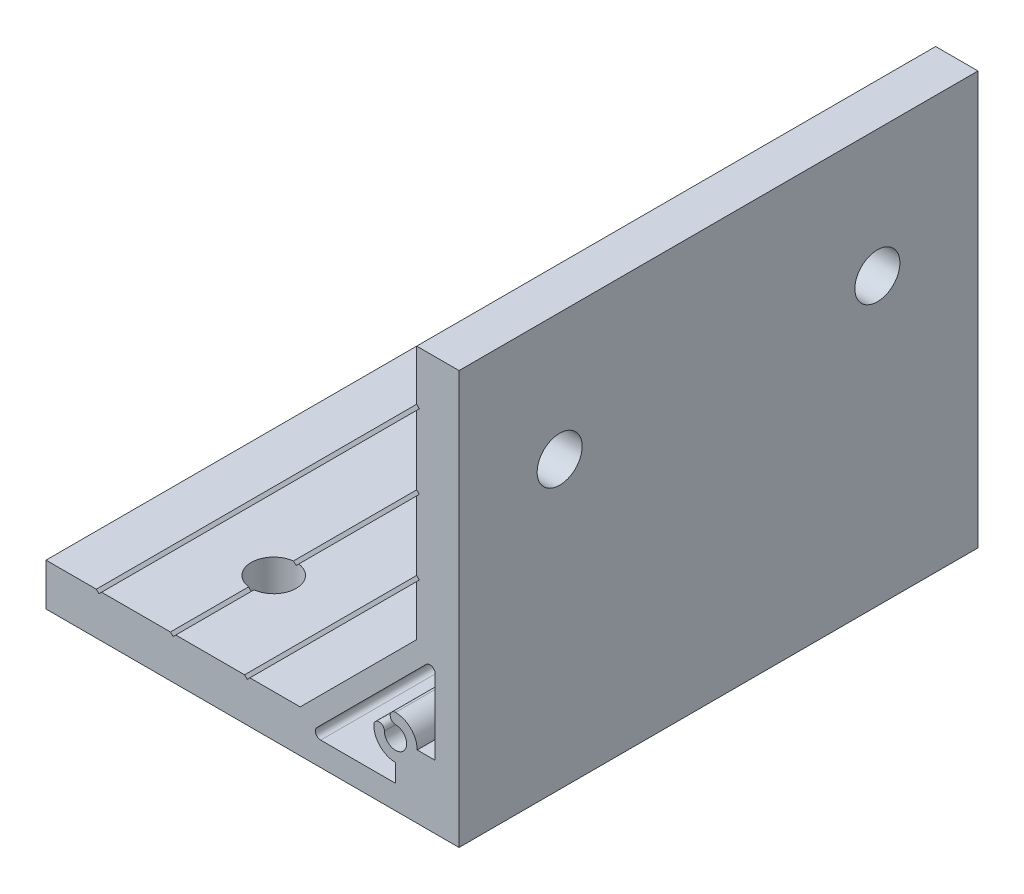
SolidWorks part; units mm, degrees
material "6063 T5"
ref_plane "Спереди" through (0, 0, 0) normal (0, 0, 1) x (1, 0, 0)
ref_plane "Сверху" through (0, 0, 0) normal (0, 1, 0) x (1, 0, 0)
ref_plane "Справа" through (0, 0, 0) normal (1, 0, 0) x (0, 0, -1)
sketch "Эскиз1" plane through (0, 0, 0) normal (0, 0, 1) x (1, 0, 0)
  line L0 (-78, 0) -> (0, 0)
  line L1 (0, 0) -> (0, 78)
  line L3 (-8, 53.5) -> (-8, 40.5)
  line L4 (-8, 40.5) -> (-7.5, 40)
  line L5 (-7.5, 40) -> (-8, 39.5)
  line L6 (-8, 39.5) -> (-8, 30)
  line L7 (-8, 30) -> (-30, 8)
  line L8 (-30, 8) -> (-39.5, 8)
  line L9 (-39.5, 8) -> (-40, 7.5)
  line L10 (-40, 7.5) -> (-40.5, 8)
  line L11 (-40.5, 8) -> (-53.5, 8)
  line L13 (-4.5, 12) -> (-4.5, 26.136)
  line L14 (-6.2071, 26.8431) -> (-26.8431, 6.2071)
  line L15 (-26.136, 4.5) -> (-12, 4.5)
  line L16 (-12, 4.5) -> (-12, 7.9)
  line L17 (-7.9, 12) -> (-4.5, 12)
  line L18 (-8, 53.5) -> (-7.5, 54)
  line L19 (-7.5, 54) -> (-8, 54.5)
  line L20 (-8, 54.5) -> (-8, 67.5)
  line L21 (-8, 67.5) -> (-7.5, 68)
  line L22 (-7.5, 68) -> (-8, 68.5)
  line L23 (-8, 68.5) -> (-8, 78)
  line L24 (-8, 78) -> (0, 78)
  line L25 (-53.5, 8) -> (-54, 7.5)
  line L26 (-54, 7.5) -> (-54.5, 8)
  line L27 (-54.5, 8) -> (-67.5, 8)
  line L28 (-67.5, 8) -> (-68, 7.5)
  line L29 (-68, 7.5) -> (-68.5, 8)
  line L30 (-68.5, 8) -> (-78, 8)
  line L31 (-78, 8) -> (-78, 0)
  arc A0 (-4.5, 26.136) -> (-6.2071, 26.8431) centre (-5.5, 26.136) ccw
  arc A1 (-26.8431, 6.2071) -> (-26.136, 4.5) centre (-26.136, 5.5) ccw
  arc A2 (-12, 7.9) -> (-16.1, 12) centre (-12, 12) cw
  arc A3 (-16.1, 12) -> (-14.1, 12) centre (-15.1, 12) cw
  arc A4 (-14.1, 12) -> (-12, 14.1) centre (-12, 12) ccw
  arc A5 (-12, 14.1) -> (-12, 16.1) centre (-12, 15.1) cw
  arc A6 (-12, 16.1) -> (-7.9, 12) centre (-12, 12) cw
  dimension "D6" = 4.2
  dimension "D7" = 1
  dimension "D9" = 1
  dimension "D2" = 8
  dimension "D3" = 135
  dimension "D4" = 12
  dimension "D5" = 12
  dimension "D8" = 30
  dimension "D10" = 3.5
  dimension "D11" = 4.5
  dimension "D12" = 40
  dimension "D13" = 1
  dimension "D14" = 54
  dimension "D15" = 68
  dimension "D16" = 78
extrude "Бобышка-Вытянуть1" add sketch "Эскиз1" along normal mid plane 98
sketch "Эскиз2" plane through (-8, 0, 0) normal (-1, 0, 0) x (0, 0, 1)
  line L1 (49, 54) -> (-49, 54) construction
  line L2 (-30, 54) -> (30, 54) construction
  circle A0 centre (-30, 54) radius 4.25
  circle A1 centre (30, 54) radius 4.25
  point P2 (0, 54)
  dimension "D1" = 8.5
  dimension "D2" = 60
extrude "Вырез-Вытянуть1" cut sketch "Эскиз2" against normal through all
sketch "Эскиз3" plane through (0, 8, 0) normal (0, 1, 0) x (1, 0, 0)
  line L1 (-54, -49) -> (-54, 49) construction
  line L2 (-54, 30) -> (-54, -30) construction
  circle A0 centre (-54, -30) radius 4.25
  circle A1 centre (-54, 30) radius 4.25
  point P2 (-54, 0)
  dimension "D1" = 8.5
  dimension "D2" = 60
extrude "Вырез-Вытянуть2" cut sketch "Эскиз3" against normal through all
